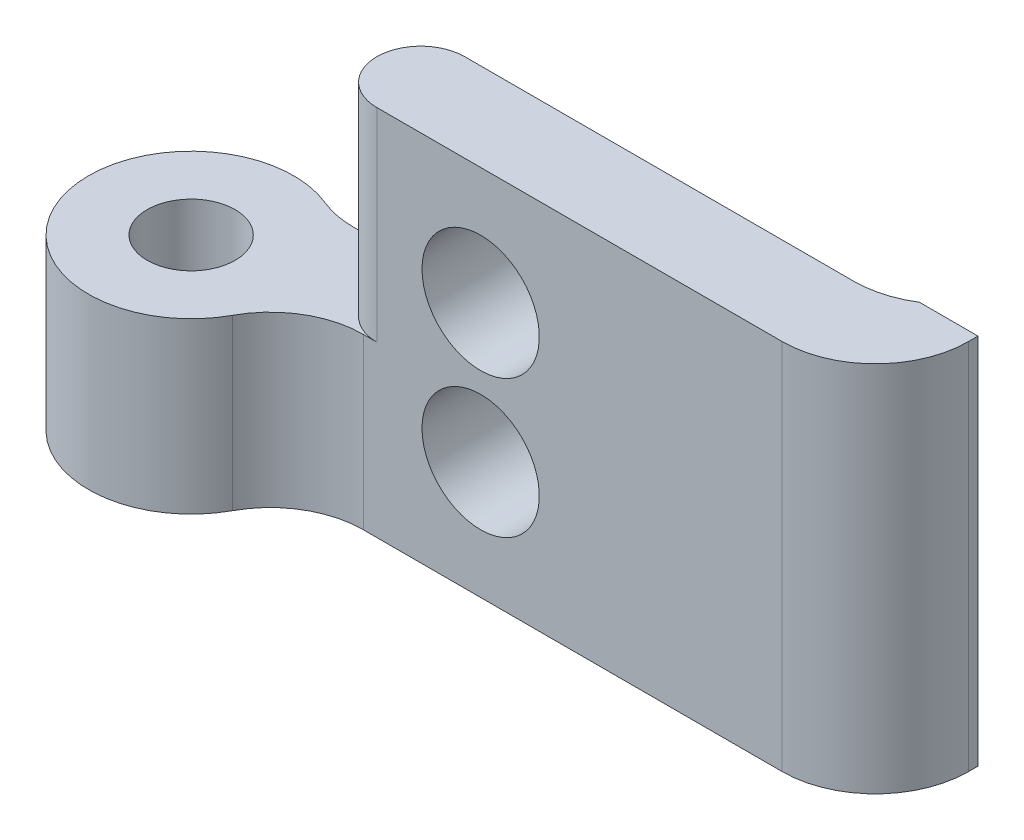
SolidWorks part; units mm, degrees
ref_plane "Front Plane" through (0, 0, 0) normal (0, 0, 1) x (1, 0, 0)
ref_plane "Top Plane" through (0, 0, 0) normal (0, 1, 0) x (1, 0, 0)
ref_plane "Right Plane" through (0, 0, 0) normal (1, 0, 0) x (0, 0, -1)
sketch "Sketch1" plane through (0, 0, 0) normal (0, 1, 0) x (1, 0, 0)
  line L0 (-18.5638, 11.2355) -> (1.2664, 11.2355)
  line L1 (1.2664, 11.2355) -> (1.2664, 14.2355)
  line L2 (1.2664, 14.2355) -> (-20.261, 14.2355)
  line L5 (1.2664, 15.2355) -> (1.2664, 18.2355) construction
  line L6 (-22.0638, 15.2355) -> (1.2664, 15.2355) construction
  circle A0 centre (-22.0638, 11.2355) radius 3.5
  dimension "D1" = 7
  dimension "D2" = 3
  dimension "D3" = 1
extrude "Boss-Extrude1" add sketch "Sketch1" along normal blind 12.7
sketch "Sketch2" plane through (0, 12.7, 0) normal (0, 1, 0) x (1, 0, 0)
  line L0 (-18.5638, 11.2355) -> (1.2664, 11.2355) construction
  line L1 (1.2664, 14.2355) -> (-20.261, 14.2355) construction
  line L2 (-15.7336, 11.2355) -> (-15.7336, 14.2355) construction
  line L3 (1.2664, 11.2355) -> (1.2664, 14.2355) construction
  line L4 (-15.7336, 11.2355) -> (-15.7336, 4.0688)
  line L5 (-15.7336, 4.0688) -> (-31.2061, 4.0688)
  line L6 (-31.2061, 4.0688) -> (-31.2061, 17.9688)
  line L7 (-31.2061, 17.9688) -> (-15.7336, 17.9688)
  line L8 (-15.7336, 17.9688) -> (-15.7336, 14.2355)
  arc A0 (-15.7336, 11.2355) -> (-15.7336, 14.2355) centre (-15.7336, 12.7355) cw
  dimension "D1" = 17
extrude "Cut-Extrude1" cut sketch "Sketch2" against normal up to surface (6.93 mm away)
sketch "Sketch3" plane through (0, 5.77, 0) normal (0, 1, 0) x (1, 0, 0)
  circle A0 centre (-22.0638, 11.2355) radius 1.5
  arc A1 (-20.261, 14.2355) -> (-18.5638, 11.2355) centre (-22.0638, 11.2355) ccw construction
  dimension "D1" = 3
extrude "Cut-Extrude2" cut sketch "Sketch3" against normal through all
sketch "Sketch4" plane through (0, 12.7, 0) normal (0, 1, 0) x (1, 0, 0)
  line L0 (1.2664, 14.2355) -> (1.2664, 14.7355)
  line L1 (1.2664, 14.7355) -> (-0.7336, 14.7355)
  line L2 (-0.7336, 14.7355) -> (-0.7336, 14.2355)
  line L3 (1.2664, 14.2355) -> (-15.7336, 14.2355) construction
  line L4 (-0.7336, 14.2355) -> (1.2664, 14.2355)
  arc A0 (-0.7336, 14.7355) -> (-2.4728, 14.2355) centre (-2.4728, 17.5105) cw
  line M4 (1.2664, 14.2355) -> (-15.7336, 14.2355)
  dimension "D3" = 3.275
  dimension "D1" = 0.5
  dimension "D2" = 2
extrude "Boss-Extrude2" add sketch "Sketch4" against normal up to surface (12.7 mm away) contours L1 L2 L0 M4 | L2 A0 M4 up to face at (-22.0638, 0, -9.7355)
fillet "Fillet1" radius 3.175 3 edges at (1.2664, 6.35, -11.2355) (-20.261, 2.885, -14.2355) (-18.5638, 2.885, -11.2355)
sketch "Sketch5" plane through (0, 0, -14.2355) normal (0, 0, -1) x (-1, 0, 0)
  circle A0 centre (12.1922, 8.7) radius 2
  circle A1 centre (12.1922, 4) radius 2
  dimension "D1" = 4
extrude "Cut-Extrude3" cut sketch "Sketch5" against normal blind 10
sketch "Sketch6" plane through (0, 0, -14.2355) normal (0, 0, -1) x (-1, 0, 0)
  circle A0 centre (4.7336, 6.35) radius 1.585
  circle A1 centre (4.7336, 6.35) radius 1.585 construction
extrude "Cut-Extrude4" cut sketch "Sketch6" against normal blind 1.5
